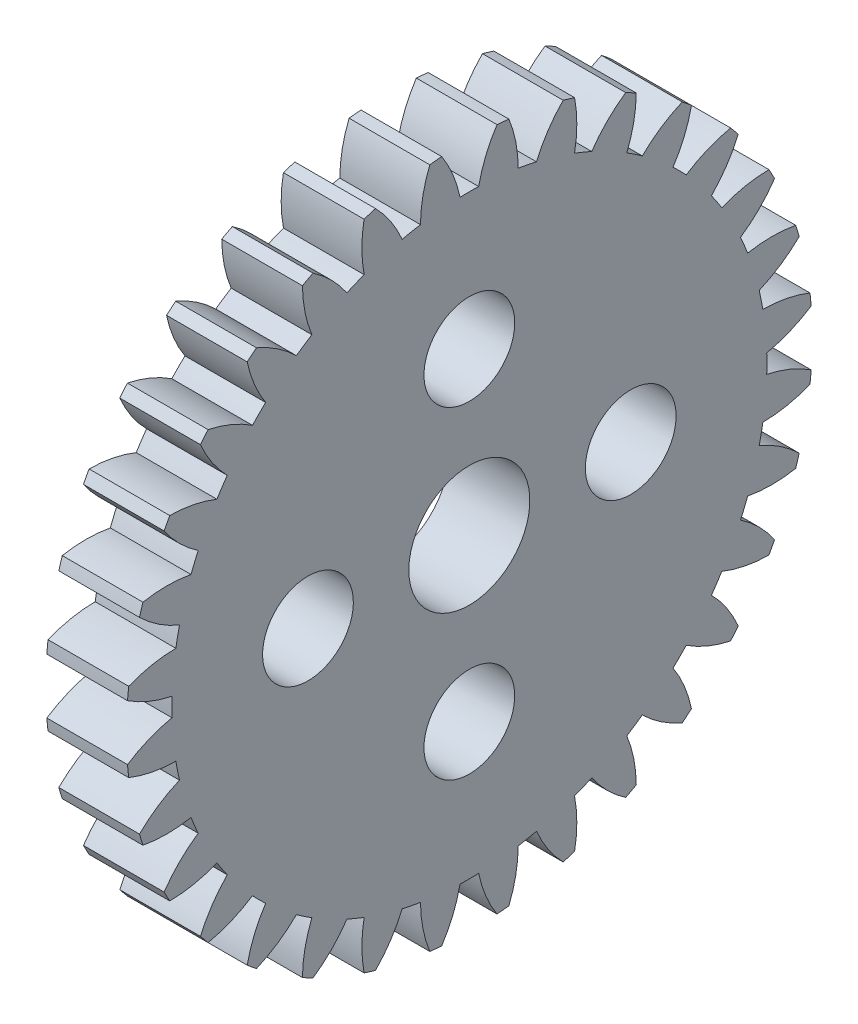
SolidWorks part; units mm, degrees
ref_plane "Plane1" through (0, 0, 0) normal (0, 0, 1) x (1, 0, 0)
ref_plane "Plane2" through (0, 0, 0) normal (0, 1, 0) x (1, 0, 0)
ref_plane "Plane3" through (0, 0, 0) normal (1, 0, 0) x (0, 0, -1)
sketch "HoldingSke" plane through (0, 0, 0) normal (0, 1, 0) x (1, 0, 0)
  line L0 (0, 0) -> (0.848, -0.5299)
  line L1 (-15, 0) -> (100, 0) construction
  line L2 (0, 0) -> (-2.1039, 2.3779)
  line L3 (0, 0) -> (-11.863, 4.5341)
  line L4 (0, 0) -> (7.3237, 4.5764)
  line L5 (0, 0) -> (-46.8476, -17.4728)
  line L6 (0, 0) -> (-3.3159, -2.2372)
  line L7 (-2.1039, 2.3779) -> (8.6586, 51.2059)
  line L8 (-76.2, 54.61) -> (-75.2, 54.61)
  line L9 (-71.009, 38.7566) -> (-53.1078, 45.2721)
  line L10 (-76.2, 71.12) -> (104.1128, 71.12)
  line L11 (0, 0) -> (-4, 0)
  line L12 (-76.2, 101.6) -> (-76.162, 101.6)
  line L13 (24.9733, 27.94) -> (52.9518, 28.4284)
  line L14 (24.9733, 27.94) -> (24.9743, 27.94)
  line L15 (24.9733, 27.94) -> (100.4006, 29.5858)
  line L16 (-63.627, -1) -> (-12.827, -1)
  circle A0 centre (0, 0) radius 3
  circle A1 centre (0, 0) radius 14.749
  circle A2 centre (0, 0) radius 37.5
  circle A3 centre (0, 0) radius 3
  dimension "MHD" = 29.498
  dimension "Hub_dia" = 75
  dimension "Bore" = 6
  dimension "MBD" = 6
  dimension "Num_teeth" = 32
  dimension "Pitch" = 1
  dimension "Overall_len" = 50
  dimension "Show_teeth" = 32
  dimension "Thickness" = 4
  dimension "OAL" = 50.0001
  dimension "T_dim" = 1
  dimension "Ap" = 20
  dimension "H" = 19.05
  dimension "Pitch_radius" = 180.3128
  dimension "Width" = 4
  dimension "Backlash" = 0.038
  dimension "Addendum_fac" = 1
  dimension "Dedendum_fac" = 1.25
  dimension "Clearance_fac" = 0.25
  dimension "Dedendum_add" = 0.001
  dimension "Module" = 1
sketch "BasProSke" plane through (0, 0, 0) normal (0, 1, 0) x (1, 0, 0)
  line L0 (-10, 0) -> (60, 0) construction
  line L1 (0, 0) -> (0, 17)
  line L2 (0, 0) -> (4, 0)
  line L3 (4, 0) -> (4, 17)
  line L4 (4, 17) -> (0, 17)
  dimension "Thickness" = 4
  dimension "Diameter" = 34
revolve "Base-Revolve" add sketch "BasProSke" angle 360 about L0
sketch "TooCutSke" plane through (0, 0, 0) normal (1, 0, 0) x (0, 0, -1)
  line L1 (0, 0) -> (0, 107) construction
  line L2 (0, 0) -> (-0.8516, 15.9773) construction
  line L3 (0, 0) -> (-3.1334, 31.8138) construction
  line L4 (-0.8516, 15.9773) -> (-1.5667, 15.9069) construction
  arc A0 (0.462, 14.7418) -> (-0.462, 14.7418) centre (0, 0) ccw
  arc A1 (1.3867, 16.9688) -> (-1.3867, 16.9688) centre (0, 0) ccw
  circle A2 centre (0, 0) radius 16 construction
  circle A3 centre (0, 0) radius 15.0351 construction
  arc A4 (-0.462, 14.7418) -> (-1.3867, 16.9688) centre (-6.7293, 13.4451) ccw
  arc A5 (1.3867, 16.9688) -> (0.462, 14.7418) centre (6.7293, 13.4451) ccw
  dimension "Root_dia" = 29.498
  dimension "Overcut_dia" = 34.0508
  dimension "Pitch_dia" = 32
  dimension "Base_dia" = 30.0702
  dimension "Flank_rad" = 6.4
  dimension "Half_ang" = 5.625
  dimension "Half_CT" = 0.7186
extrude "ToothCut" cut sketch "TooCutSke" along normal through all
fillet "Breaks" [suppressed] radius 0.02
fillet "RootFillets" [suppressed] radius 0.251
pattern_circular "TeethCuts" count 32 every 11.25 about axis through (-10, 0, 0) along (1, 0, 0) of "ToothCut", "RootFillets", "Breaks"
sketch "HubNeaOneSke" plane through (0, 0, 0) normal (-1, 0, 0) x (0, 0, 1)
  circle A0 centre (0, 0) radius 14.749
  dimension "Diameter" = 29.498
extrude "HubNearOne" [suppressed] add sketch "HubNeaOneSke" along normal blind 46.0001
sketch "HubNeaBotSke" plane through (0, 0, 0) normal (-1, 0, 0) x (0, 0, 1)
  circle A0 centre (0, 0) radius 14.749
  dimension "Diameter" = 29.498
extrude "HubNearBoth" [suppressed] add sketch "HubNeaBotSke" along normal blind 23
ref_plane "FarPln" through (4, 0, 0) normal (1, 0, 0) x (0, 0, -1)
sketch "HubFarSke" plane through (4, 0, 0) normal (1, 0, 0) x (0, 0, -1)
  circle A0 centre (0, 0) radius 14.749
  dimension "Diameter" = 29.498
extrude "HubFar" [suppressed] add sketch "HubFarSke" along normal blind 23
sketch "BorSke" plane through (0, 0, 0) normal (1, 0, 0) x (0, 0, -1)
  circle A0 centre (0, 0) radius 3
  dimension "Diameter" = 6
extrude "Bore" cut sketch "BorSke" along normal mid plane 100.0001
sketch "KeySke" plane through (0, 0, 0) normal (1, 0, 0) x (0, 0, -1)
  line L0 (-1, 0) -> (-1, 4)
  line L1 (-1, 4) -> (1, 4)
  line L2 (1, 4) -> (1, 0)
  line L3 (0, 0) -> (0, 34) construction
  line L4 (-1, 0) -> (1, 0)
  dimension "Offset" = 4
  dimension "Width" = 2
extrude "Keyway" [suppressed] cut sketch "KeySke" along normal mid plane 100.0001
pattern_circular "Keyway2" [suppressed] count 2 every 90 about axis through (-10, 0, 0) along (1, 0, 0)
hole_wizard "M4 Clearance Hole1" positions "Sketch1" profile "Sketch2" hole size "M4" standard "ANSI Metric" end condition through all
sketch "Sketch1" plane through (4, 0, 0) normal (1, 0, 0) x (0, 0, -1)
  line L2 (0, 0) -> (0, 8) construction
  point P9 (0, 8)
  dimension "D1" = 8
sketch "Sketch2" plane through (4, 8, 0) normal (0, 1, 0) x (0, 0, -1)
  line L0 (0, 0) -> (0, 4)
  line L1 (0, 4) -> (2.25, 4)
  line L2 (2.25, 4) -> (2.25, 0)
  line L5 (2.25, 0) -> (0, 0)
  line L11 (0, -6.35) -> (0, 107.95) construction
  dimension "Thru Hole Dia." = 4.5
  dimension "Thru Hole Depth" = 4
pattern_circular "CirPattern1" count 4 over 360 about axis through (0, 0, 0) along (1, 0, 0) of "M4 Clearance Hole1"
equation "' \"Module@HoldingSke\" = 6.35"
equation "' \"Num_teeth@HoldingSke\" = 12"
equation "' \"Ap@HoldingSke\" =  20"
equation "' \"Ap@HoldingSke\" = 20"
equation "' \"Width@HoldingSke\" = 0.5 * 25.4"
equation "' \"Hub_dia@HoldingSke\"= 1 * 25.4"
equation "' \"Hub_dia@HoldingSke\" = 1 * 25.4"
equation "' \"Overall_len@HoldingSke\" = 1.0 * 25.4"
equation "' \"Bore@HoldingSke\" = 0.75 * 25.4"
equation "' \"T_dim@HoldingSke\" = 0.1 * 25.4"
equation "' \"Width@KeySke\" = 0.25 * 25.4"
equation "' \"Show_teeth@HoldingSke\" = 13"
equation "' \"Backlash@HoldingSke\" = 0.009 * 25.4"
equation "' \"Addendum_fac@HoldingSke\" = 1.0"
equation "' \"Dedendum_fac@HoldingSke\" = 1.25"
equation "' \"Dedendum_add@HoldingSke\" = 0.00005 * 25.4"
equation "' \"Clearance_fac@HoldingSke\" = 0.25"
equation "\"Pitch@HoldingSke\" = 1 / \"Module@HoldingSke\""
equation "\"Overcut_dia@TooCutSke\" = (\"Num_teeth@HoldingSke\" + 2 * \"Addendum_fac@HoldingSke\") / \"Pitch@HoldingSke\" + 0.002 * 25.4"
equation "\"Pitch_dia@TooCutSke\" = \"Num_teeth@HoldingSke\" / \"Pitch@HoldingSke\""
equation "\"Base_dia@TooCutSke\" = \"Num_teeth@HoldingSke\" / \"Pitch@HoldingSke\" * cos((\"Ap@HoldingSke\"  * 3.14159265 / 180))"
equation "\"Root_dia@TooCutSke\" = (\"Num_teeth@HoldingSke\" + 2) / \"Pitch@HoldingSke\" - 2 * (\"Addendum_fac@HoldingSke\" + \"Dedendum_fac@HoldingSke\") / \"Pitch@HoldingSke\" - \"Dedendum_add@HoldingSke\" * 2"
equation "\"Half_ang@TooCutSke\" = 180 / \"Num_teeth@HoldingSke\""
equation "\"Half_CT@TooCutSke\" = \"Num_teeth@HoldingSke\" / \"Pitch@HoldingSke\" * sin((3.14159265 / 2 / \"Num_teeth@HoldingSke\")) / 2 - 7 * \"Backlash@HoldingSke\" / 4"
equation "\"Flank_rad@TooCutSke\" = \"Num_teeth@HoldingSke\" / \"Pitch@HoldingSke\" / 5"
equation "\"Radius@RootFillets\" = \"Clearance_fac@HoldingSke\" / \"Pitch@HoldingSke\" + \"Dedendum_add@HoldingSke\""
equation "\"Break_rad@Breaks\" = 0.02 / \"Pitch@HoldingSke\""
equation "\"Thickness@HoldingSke\" = \"Width@HoldingSke\""
equation "\"OAL@HoldingSke\" = \"Thickness@HoldingSke\""
equation "\"MHD@HoldingSke\" = (\"Num_teeth@HoldingSke\" + 2) / \"Pitch@HoldingSke\" - 2 * (\"Addendum_fac@HoldingSke\" + \"Dedendum_fac@HoldingSke\")  / \"Pitch@HoldingSke\" - \"Dedendum_add@HoldingSke\" * 2"
equation "\"MBD@HoldingSke\" = (\"Num_teeth@HoldingSke\" + 2) / \"Pitch@HoldingSke\" - 2 * (\"Addendum_fac@HoldingSke\" + \"Dedendum_fac@HoldingSke\")  / \"Pitch@HoldingSke\" - \"Dedendum_add@HoldingSke\" * 2 - 0.002 * 25.4"
equation "\"MHD@HoldingSke\" = ((sgn( \"MHD@HoldingSke\" - \"Hub_dia@HoldingSke\" )-1)*( \"MHD@HoldingSke\" - \"Hub_dia@HoldingSke\" ))/-2+ \"Hub_dia@HoldingSke\""
equation "\"MBD@HoldingSke\" = ((sgn( \"MBD@HoldingSke\" - \"Bore@HoldingSke\" )-1)*( \"MBD@HoldingSke\" - \"Bore@HoldingSke\" ))/-2+ \"Bore@HoldingSke\""
equation "\"OAL@HoldingSke\" = ((sgn( \"OAL@HoldingSke\" - \"Overall_len@HoldingSke\" )+1)*( \"OAL@HoldingSke\" - \"Overall_len@HoldingSke\" ))/2 + \"Overall_len@HoldingSke\" + 0.000002 * 25.4"
equation "\"Num_teeth@TeethCuts\" = int( \"Show_teeth@HoldingSke\" ) + 1"
equation "\"Num_teeth@TeethCuts\" = ((sgn( \"Num_teeth@TeethCuts\" - \"Num_teeth@HoldingSke\" )-1)*( \"Num_teeth@TeethCuts\" - \"Num_teeth@HoldingSke\" ))/-2+ \"Num_teeth@HoldingSke\""
equation "\"Num_teeth@TeethCuts\" = ((sgn( \"Num_teeth@TeethCuts\" - 2.0)+1)*( \"Num_teeth@TeethCuts\" - 2.0))/2 +2.0"
equation "\"Angle@TeethCuts\" = 360.0 / \"Num_teeth@HoldingSke\""
equation "\"Diameter@BasProSke\" = (\"Num_teeth@HoldingSke\" + 2 * \"Addendum_fac@HoldingSke\") / \"Pitch@HoldingSke\""
equation "\"Thickness@BasProSke\"  = \"Thickness@HoldingSke\""
equation "' \"Fillet_rad@BasProSke\" =  \"Thickness@HoldingSke\" * 0.05"
equation "' \"Fillet_rad@BasProSke\" = \"Thickness@HoldingSke\" * 0.05"
equation "\"MHD@HoldingSke\" = ((sgn( \"MHD@HoldingSke\" - \"Root_dia@TooCutSke\" )-1)*( \"MHD@HoldingSke\" - \"Root_dia@TooCutSke\" ))/-2+ \"Root_dia@TooCutSke\""
equation "\"Diameter@HubNeaOneSke\" = \"MHD@HoldingSke\""
equation "\"Length@HubNearOne\" = \"OAL@HoldingSke\" - \"Thickness@BasProSke\""
equation "\"Diameter@HubNeaBotSke\" = \"MHD@HoldingSke\""
equation "\"Length@HubNearBoth\" = ( \"OAL@HoldingSke\" - \"Thickness@BasProSke\" ) / 2.0"
equation "\"Thickness@FarPln\" = \"Thickness@BasProSke\""
equation "\"Diameter@HubFarSke\" = \"MHD@HoldingSke\""
equation "\"Length@HubFar\" = ( \"OAL@HoldingSke\" - \"Thickness@BasProSke\" ) / 2.0"
equation "\"Diameter@BorSke\" = \"MBD@HoldingSke\""
equation "\"D1@Bore\" = \"OAL@HoldingSke\" * 2.0"
equation "\"D1@Keyway\" = \"OAL@HoldingSke\" * 2.0"
equation "\"Offset@KeySke\" = \"T_dim@HoldingSke\" + \"MBD@HoldingSke\" / 2.0"
